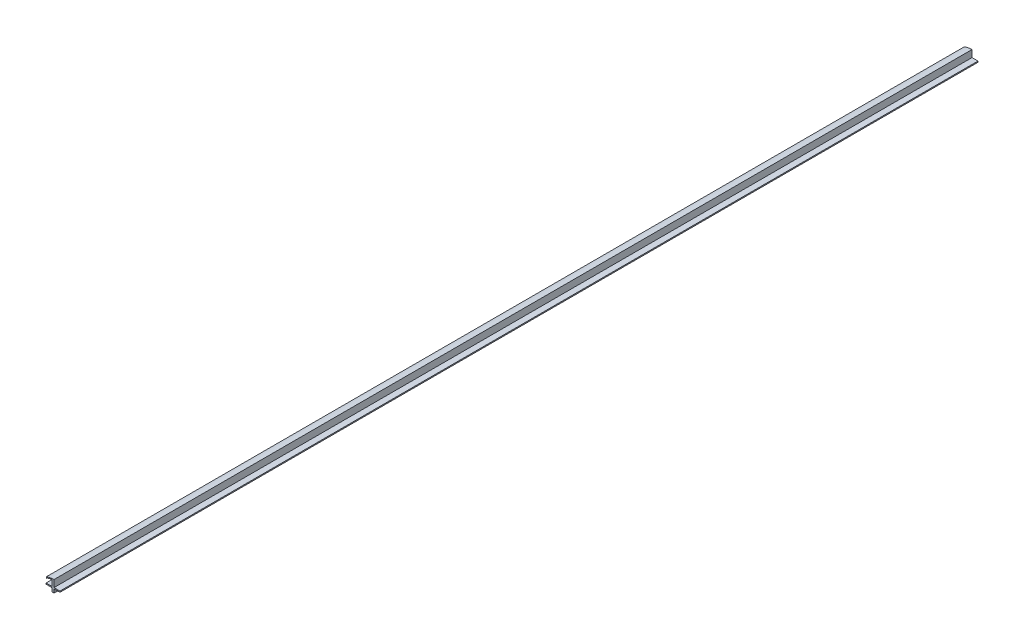
SolidWorks part; units mm, degrees
material "Pure Lead"
ref_plane "Front Plane" through (0, 0, 0) normal (0, 0, 1) x (1, 0, 0)
ref_plane "Top Plane" through (0, 0, 0) normal (0, 1, 0) x (1, 0, 0)
ref_plane "Right Plane" through (0, 0, 0) normal (1, 0, 0) x (0, 0, -1)
sketch "Sketch1" plane through (0, 0, 0) normal (0, 0, 1) x (1, 0, 0)
  line L0 (1169.5811, 22.86) -> (1169.5811, 18.542)
  line L1 (1169.5811, 32.258) -> (1169.5811, 24.13)
  line L2 (1167.2189, 22.86) -> (1167.2189, 18.542)
  line L3 (1167.2189, 30.988) -> (1167.2189, 24.13)
  line L4 (1176.528, 24.13) -> (1169.5811, 24.13)
  line L5 (1160.272, 24.13) -> (1167.2189, 24.13)
  line L6 (1169.5811, 18.542) -> (1167.2189, 18.542)
  line L7 (1176.528, 24.13) -> (1176.528, 22.86)
  line L8 (1160.272, 24.13) -> (1160.272, 22.86)
  line L9 (1160.272, 32.258) -> (1160.272, 30.988) construction
  line L10 (1169.5811, 32.258) -> (1160.272, 32.258) construction
  line L11 (1160.272, 30.988) -> (1167.2189, 30.988) construction
  line L12 (1169.5811, 22.86) -> (1176.528, 22.86)
  line L13 (1160.272, 22.86) -> (1167.2189, 22.86)
  line L14 (1160.272, 30.988) -> (1160.272, 29.718) construction
  line L15 (1160.272, 30.988) -> (1160.6956, 29.7907) construction
  line L16 (1160.4838, 30.3894) -> (1160.9074, 29.1921)
  arc A0 (1169.5811, 32.258) -> (1160.272, 30.988) centre (1169.5811, -2.4949) ccw construction
  arc A1 (1167.2189, 30.988) -> (1160.6956, 29.7907) centre (1167.2189, 12.6184) ccw construction
  arc A2 (1169.5811, 32.258) -> (1160.4838, 30.3894) centre (1169.5811, 9.179) ccw
  arc A3 (1167.2189, 30.988) -> (1160.9074, 29.1921) centre (1167.2189, 18.9996) ccw
extrude "Extrude1" add sketch "Sketch1" along normal mid plane 1066.8
